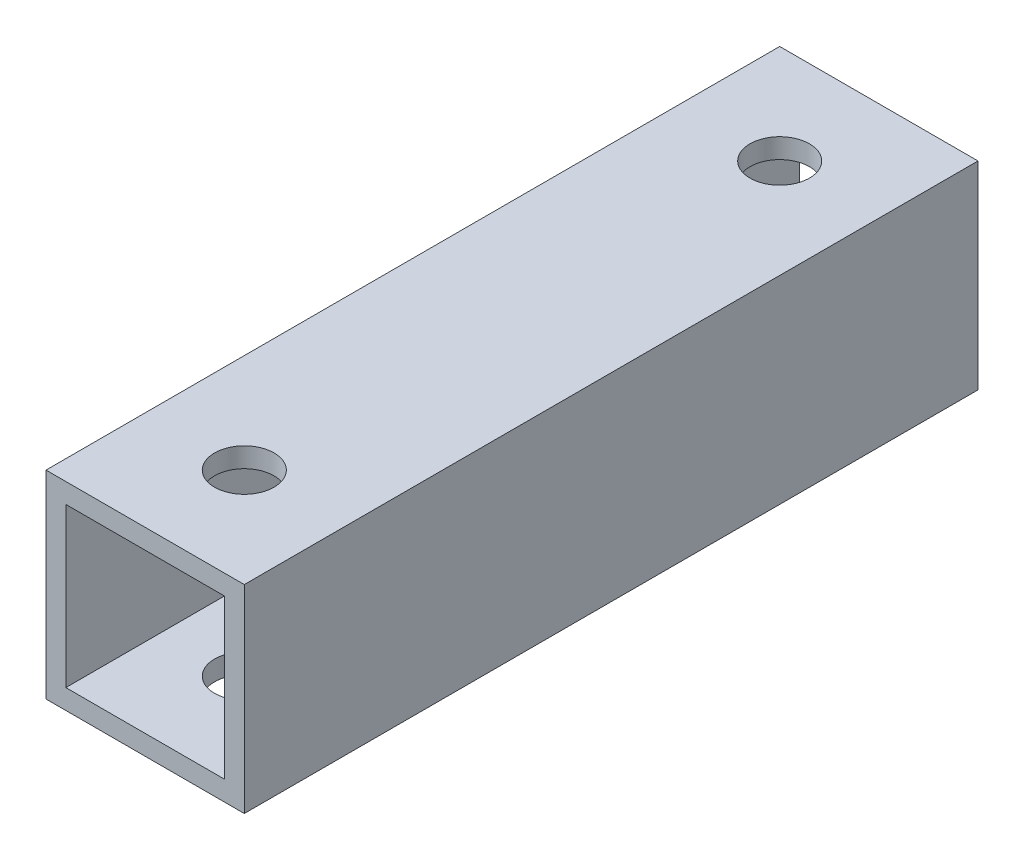
SolidWorks part; units mm, degrees
material "6063-O"
ref_plane "前视基准面" through (0, 0, 0) normal (0, 0, 1) x (1, 0, 0)
ref_plane "上视基准面" through (0, 0, 0) normal (0, 1, 0) x (1, 0, 0)
ref_plane "右视基准面" through (0, 0, 0) normal (1, 0, 0) x (0, 0, -1)
other "Configuration Table"
sketch "草图1" plane through (0, 0, 0) normal (0, 0, 1) x (1, 0, 0)
  line L1 (7.3178, -99.5865) -> (17.3178, -99.5865)
  line L2 (7.3178, -99.5865) -> (7.3178, -109.5865)
  line L3 (7.3178, -109.5865) -> (17.3178, -109.5865)
  line L4 (17.3178, -99.5865) -> (17.3178, -109.5865)
  line L5 (7.3178, -99.5865) -> (17.3178, -109.5865) construction
  line L6 (7.3178, -109.5865) -> (17.3178, -99.5865) construction
  point P4 (12.3178, -104.5865)
  dimension "D1" = 10
  dimension "D2" = 10
extrude "拉伸-薄壁1" add sketch "草图1" along normal blind 37 thin
sketch "草图2" plane through (0, -109.5865, 0) normal (0, -1, 0) x (1, 0, 0)
  line L0 (12.3178, 0) -> (12.3178, 37) construction
  line L1 (7.3178, 0) -> (17.3178, 0) construction
  line L2 (7.3178, 37) -> (17.3178, 37) construction
  circle A0 centre (12.3178, 5) radius 1.5
  circle A1 centre (12.3178, 32) radius 1.5
  dimension "D1" = 5
  dimension "D2" = 5
  dimension "D3" = 3
extrude "切除-拉伸1" cut sketch "草图2" against normal blind 10
